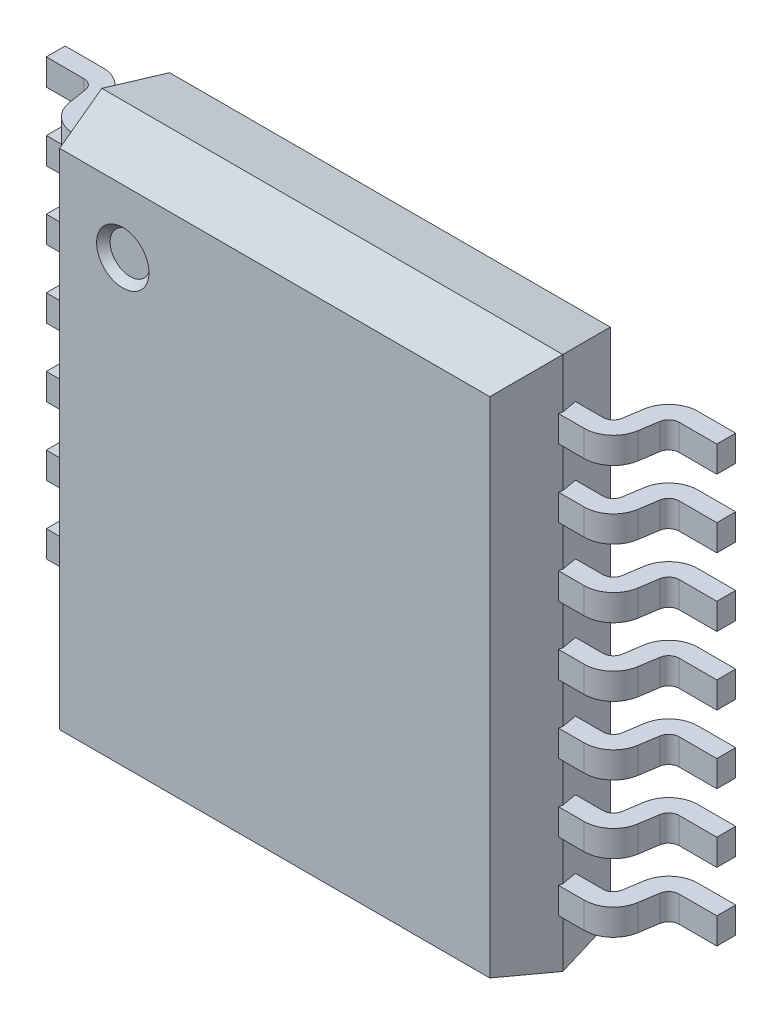
SolidWorks part; units mm, degrees
ref_plane "Спереди" through (0, 0, 0) normal (0, 0, 1) x (1, 0, 0)
ref_plane "Сверху" through (0, 0, 0) normal (0, 1, 0) x (1, 0, 0)
ref_plane "Справа" through (0, 0, 0) normal (1, 0, 0) x (0, 0, -1)
sketch "Эскиз1" plane through (0, 0, 0) normal (0, 0, 1) x (1, 0, 0)
  line L1 (-2.2, 2.55) -> (2.2, 2.55)
  line L2 (-2.2, 2.55) -> (-2.2, -2.55)
  line L3 (-2.2, -2.55) -> (2.2, -2.55)
  line L4 (2.2, 2.55) -> (2.2, -2.55)
extrude "Вытянуть1" add sketch "Эскиз1" along normal blind 0.55 draft 15 and the other way blind 0.55 draft 10 from offset 0.65
sketch "Эскиз2" plane through (0, 0, 1.2) normal (0, 0, 1) x (1, 0, 0)
  circle A0 centre (-1.45, 1.8) radius 0.25
sketch "Эскиз3" plane through (0, 0, 0) normal (0, 1, 0) x (1, 0, 0)
  line L0 (2.5354, -0.4187) -> (2.5634, -0.2372)
  line L1 (2.8402, 0) -> (3.2, 0)
  line L2 (2.8402, -0.18) -> (3.2, -0.18)
  line L3 (2.7413, -0.2647) -> (2.7133, -0.4462)
  line L4 (2.0901, -0.6835) -> (2.4366, -0.6835)
  line L5 (0, 0) -> (0, -2) construction
  line L6 (-2.0901, -0.5035) -> (-2.4366, -0.5035)
  line L7 (-2.0901, -0.5035) -> (-2.0901, -0.6835)
  line L8 (-3.2, 0) -> (-3.2, -0.18)
  line L9 (-2.0901, -0.6835) -> (-2.4366, -0.6835)
  line L10 (-2.7413, -0.2647) -> (-2.7133, -0.4462)
  line L11 (-2.8402, -0.18) -> (-3.2, -0.18)
  line L12 (3.2, 0) -> (3.2, -0.18)
  line L13 (-2.8402, 0) -> (-3.2, 0)
  line L14 (2.0901, -0.5035) -> (2.0901, -0.6835)
  line L15 (-2.5354, -0.4187) -> (-2.5634, -0.2372)
  line L16 (2.0901, -0.5035) -> (2.4366, -0.5035)
  arc A0 (2.5634, -0.2372) -> (2.8402, 0) centre (2.8402, -0.28) cw
  arc A1 (2.7133, -0.4462) -> (2.4366, -0.6835) centre (2.4366, -0.4035) cw
  arc A2 (2.5354, -0.4187) -> (2.4366, -0.5035) centre (2.4366, -0.4035) cw
  arc A3 (2.7413, -0.2647) -> (2.8402, -0.18) centre (2.8402, -0.28) cw
  arc A4 (-2.7413, -0.2647) -> (-2.8402, -0.18) centre (-2.8402, -0.28) ccw
  arc A5 (-2.5354, -0.4187) -> (-2.4366, -0.5035) centre (-2.4366, -0.4035) ccw
  arc A6 (-2.7133, -0.4462) -> (-2.4366, -0.6835) centre (-2.4366, -0.4035) ccw
  arc A7 (-2.5634, -0.2372) -> (-2.8402, 0) centre (-2.8402, -0.28) ccw
extrude "Вытянуть2" add sketch "Эскиз3" against normal blind 0.25 from offset 2.075 separate body
extrude "Вытянуть3" cut sketch "Эскиз2" against normal blind 0.07 draft 40
pattern_linear "Линейный массив1" count 7 spacing 0.65 along (0, -1, 0) of "Вытянуть2"
